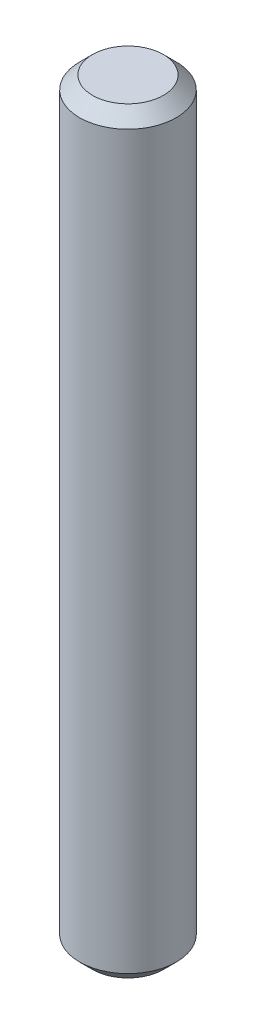
SolidWorks part; units mm, degrees
material "Stainless Steel (ferritic)"
ref_plane "Front Plane" through (0, 0, 0) normal (0, 0, 1) x (1, 0, 0)
ref_plane "Top Plane" through (0, 0, 0) normal (0, 1, 0) x (1, 0, 0)
ref_plane "Right Plane" through (0, 0, 0) normal (1, 0, 0) x (0, 0, -1)
sketch "Sketch1" plane through (0, 0, 0) normal (0, 1, 0) x (1, 0, 0)
  circle A0 centre (0, 0) radius 1.5
  dimension "D1" = 3
extrude "Boss-Extrude1" add sketch "Sketch1" along normal mid plane 23.5
chamfer "Chamfer1" distance 0.4 angle 45 2 edges at (0, -11.75, 1.5) (0, 11.75, 1.5)
